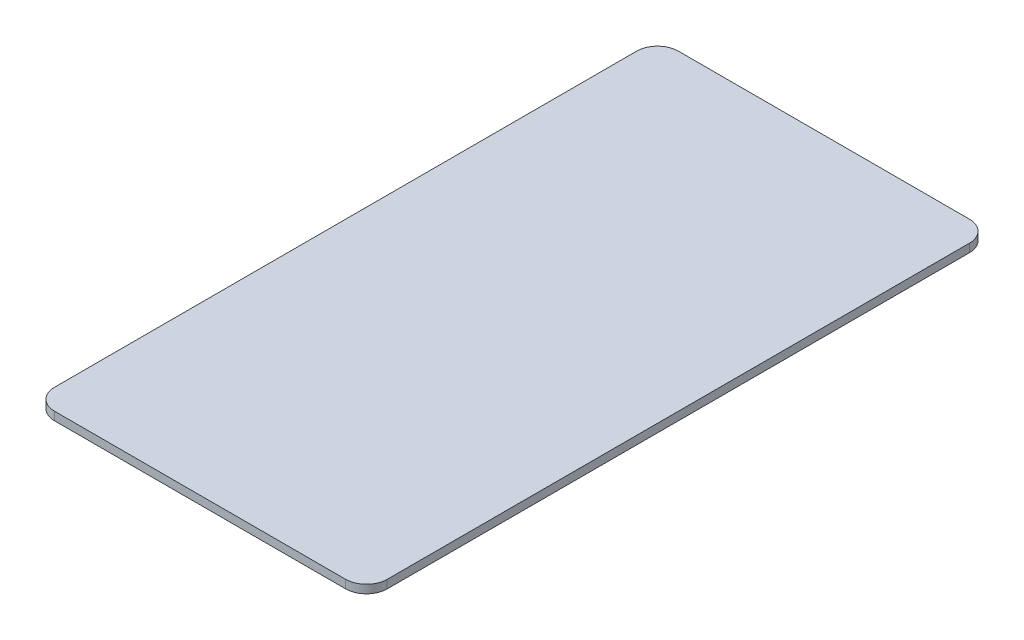
SolidWorks part; units mm, degrees
ref_plane "Front Plane" through (0, 0, 0) normal (0, 0, 1) x (1, 0, 0)
ref_plane "Top Plane" through (0, 0, 0) normal (0, 1, 0) x (1, 0, 0)
ref_plane "Right Plane" through (0, 0, 0) normal (1, 0, 0) x (0, 0, -1)
sketch "Sketch1" plane through (0, 0, 0) normal (0, 1, 0) x (1, 0, 0)
  line L1 (0, 0) -> (50.8, 0)
  line L2 (0, 0) -> (0, 95.25)
  line L3 (0, 95.25) -> (50.8, 95.25)
  line L4 (50.8, 0) -> (50.8, 95.25)
  dimension "D1" = 50.8
  dimension "D2" = 95.25
extrude "Boss-Extrude1" add sketch "Sketch1" along normal blind 1.27
fillet "Fillet1" radius 3.175 4 edges at (0, 0.635, -95.25) (50.8, 0.635, -95.25) (50.8, 0.635, 0) (0, 0.635, 0)
